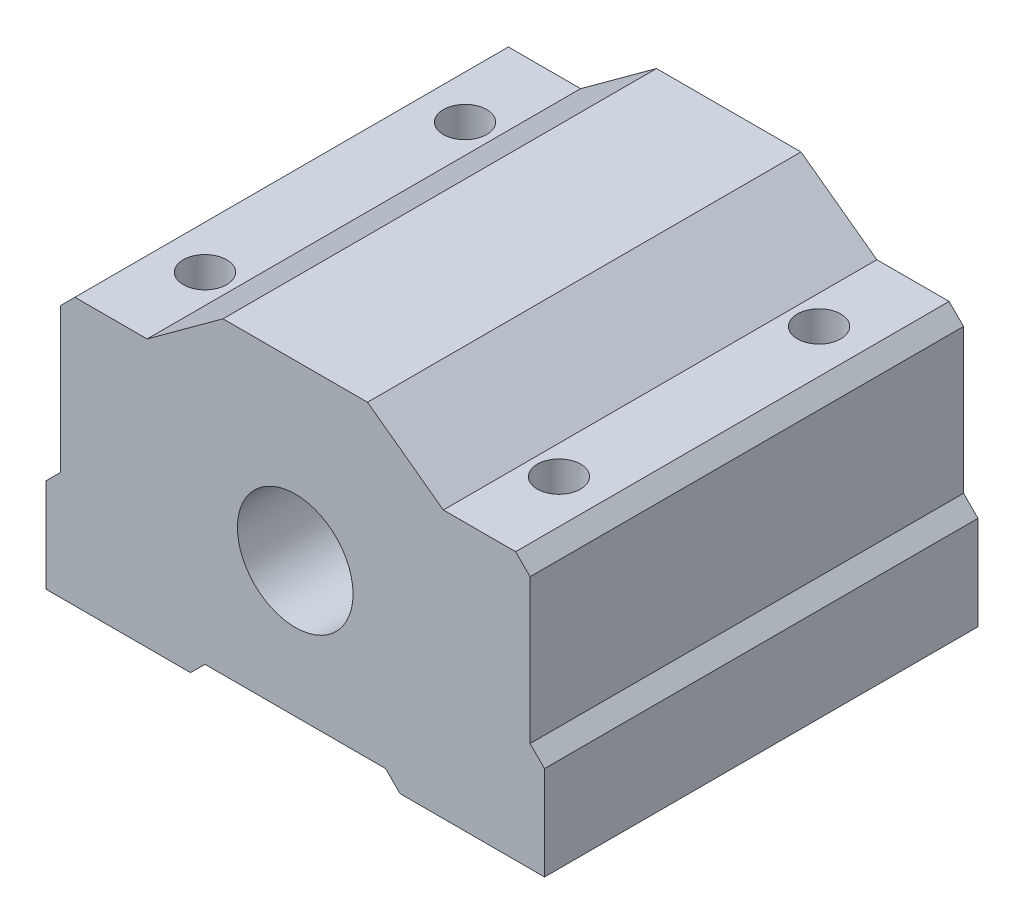
SolidWorks part; units mm, degrees
material "2014-O"
ref_plane "Front Plane" through (0, 0, 0) normal (0, 0, 1) x (1, 0, 0)
ref_plane "Top Plane" through (0, 0, 0) normal (0, 1, 0) x (1, 0, 0)
ref_plane "Right Plane" through (0, 0, 0) normal (1, 0, 0) x (0, 0, -1)
sketch "Sketch1" plane through (0, 0, 0) normal (0, 0, 1) x (1, 0, 0)
  line L0 (0, 0) -> (6.25, 0)
  line L1 (6.25, 0) -> (7.25, -1)
  line L2 (7.25, -1) -> (17.25, -1)
  line L3 (17.25, -1) -> (17.25, 5.5)
  line L4 (17.25, 5.5) -> (16.25, 6.5)
  line L5 (16.25, 6.5) -> (16.25, 16.5)
  line L6 (16.25, 16.5) -> (15.25, 17.5)
  line L7 (15.25, 17.5) -> (10.25, 17.5)
  line L8 (10.25, 17.5) -> (5, 21.3324)
  line L9 (5, 21.3324) -> (-5, 21.3324)
  line L10 (-5, 21.3324) -> (-10.25, 17.5)
  line L11 (-10.25, 17.5) -> (-15.25, 17.5)
  line L12 (-15.25, 17.5) -> (-16.25, 16.5)
  line L13 (-16.25, 16.5) -> (-16.25, 6.5)
  line L14 (-16.25, 6.5) -> (-17.25, 5.5)
  line L15 (-17.25, 5.5) -> (-17.25, -1)
  line L16 (-17.25, -1) -> (-7.25, -1)
  line L17 (-7.25, -1) -> (-6.25, 0)
  line L18 (-6.25, 0) -> (0, 0)
  dimension "D1" = 6.25
  dimension "D2" = 6.25
  dimension "D3" = 1
  dimension "D4" = 10
  dimension "D5" = 6.5
  dimension "D6" = 1
  dimension "D7" = 1
  dimension "D8" = 10
  dimension "D9" = 5
  dimension "D10" = 6.5
  dimension "D11" = 6.5
  dimension "D12" = 10
  dimension "D13" = 10
  dimension "D14" = 135
  dimension "D15" = 135
  dimension "D16" = 1
extrude "Boss-Extrude1" add sketch "Sketch1" along normal blind 30 contours L11 L12 L13 L14 L15 L16 L17 L18 L0 L1 L2 L3 L4 L5 L6 L7 L8 L9 L10
sketch "Sketch2" plane through (0, 0, 30) normal (0, 0, 1) x (1, 0, 0)
  line L0 (5, 21.3324) -> (-5, 21.3324) construction
  circle A0 centre (0, 9.3324) radius 4
  dimension "D2" = 8
  dimension "D1" = 12
extrude "Cut-Extrude1" cut sketch "Sketch2" against normal through all
sketch "Sketch3" plane through (0, 17.5, 0) normal (0, 1, 0) x (1, 0, 0)
  line L0 (15.25, 0) -> (10.25, 0) construction
  line L2 (15.25, -30) -> (10.25, -30) construction
  line L3 (16.25, -30) -> (16.25, 0) construction
  circle A0 centre (12.25, -6) radius 1.5
  circle A1 centre (12.25, -24) radius 1.5
  dimension "D3" = 3
  dimension "D4" = 3
  dimension "D6" = 4
  dimension "D1" = 6
  dimension "D2" = 4
  dimension "D5" = 6
extrude "Cut-Extrude2" cut sketch "Sketch3" against normal through all
mirror "Mirror1" about plane through (0, 0, 0) normal (1, 0, 0) of "Cut-Extrude2"
